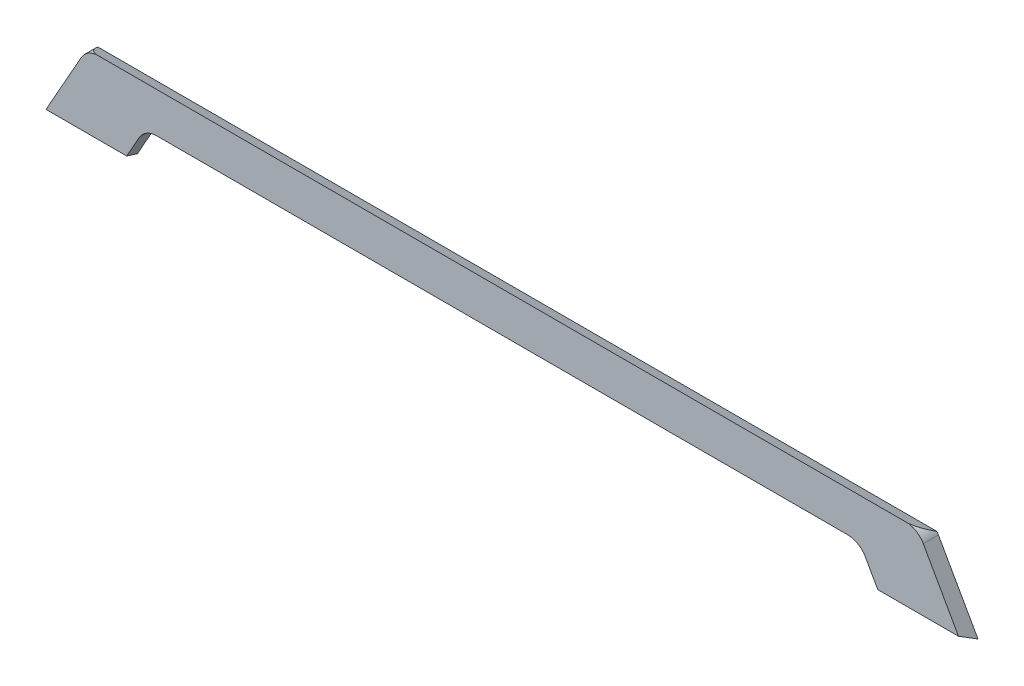
SolidWorks part; units mm, degrees
ref_plane "Front Plane" through (0, 0, 0) normal (0, 0, 1) x (1, 0, 0)
ref_plane "Top Plane" through (0, 0, 0) normal (0, 1, 0) x (1, 0, 0)
ref_plane "Right Plane" through (0, 0, 0) normal (1, 0, 0) x (0, 0, -1)
sketch "Sketch1" plane through (0, 0, 0) normal (0, 0, 1) x (1, 0, 0)
  line L0 (508, 0) -> (-508, 0)
  line L1 (-530.1336, -12.9396) -> (-579.9753, -101.4741)
  line L2 (-579.9753, -101.4741) -> (-478.3753, -101.4741)
  line L3 (-478.3753, -101.4741) -> (-457.1322, -63.7396)
  line L4 (-434.9985, -50.8) -> (434.9985, -50.8)
  line L6 (478.3753, -101.4741) -> (457.1322, -63.7396)
  line L7 (579.9753, -101.4741) -> (478.3753, -101.4741)
  line L8 (530.1336, -12.9396) -> (579.9753, -101.4741)
  arc A0 (-457.1322, -63.7396) -> (-434.9985, -50.8) centre (-434.9985, -76.2) cw
  arc A1 (-508, 0) -> (-530.1336, -12.9396) centre (-508, -25.4) ccw
  arc A2 (508, 0) -> (530.1336, -12.9396) centre (508, -25.4) cw
  arc A3 (457.1322, -63.7396) -> (434.9985, -50.8) centre (434.9985, -76.2) ccw
  dimension "D1" = 25.4
  dimension "D2" = 101.6
  dimension "D4" = 101.6
  dimension "D5" = 50.8
extrude "Boss-Extrude1" add sketch "Sketch1" along normal blind 19.05
sketch "Sketch2" plane through (0, 0, 0) normal (1, 0, 0) x (0, 0, -1)
  line L0 (0, -101.4741) -> (-60.8525, -70.2061)
  line L1 (0, -101.4741) -> (37.188, -29.1005)
  line L2 (-60.8525, -70.2061) -> (-23.6645, 2.1675)
  line L3 (37.188, -29.1005) -> (-23.6645, 2.1675)
  line L5 (84.8398, 63.6375) -> (-112.2986, 63.6375)
  line L6 (84.8398, 63.6375) -> (84.8398, -170.3284)
  line L7 (84.8398, -170.3284) -> (-112.2986, -170.3284)
  line L8 (-112.2986, 63.6375) -> (-112.2986, -170.3284)
extrude "Cut-Extrude1" cut sketch "Sketch2" against normal through all both and the other way through all
